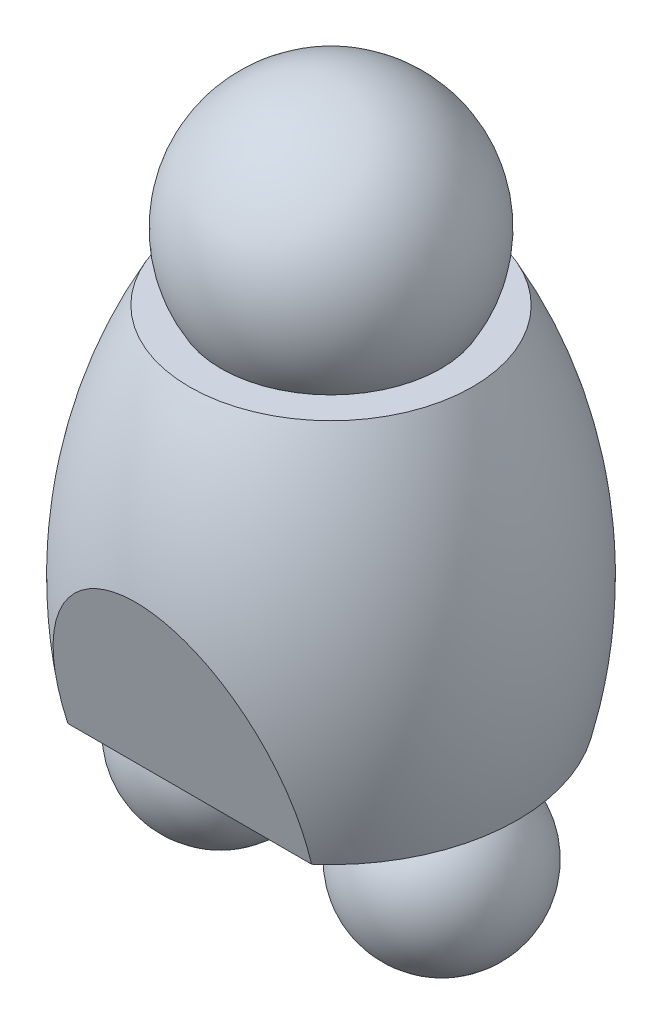
SolidWorks part; units mm, degrees
ref_plane "Front" through (0, 0, 0) normal (0, 0, 1) x (1, 0, 0)
ref_plane "Top" through (0, 0, 0) normal (0, 1, 0) x (1, 0, 0)
ref_plane "Right" through (0, 0, 0) normal (1, 0, 0) x (0, 0, -1)
sketch "Sketch1" plane through (0, 0, 0) normal (0, 0, 1) x (1, 0, 0)
  line L0 (0, 64.0999) -> (0, -73.9034) construction
  line L1 (0, 17.399) -> (0, -17.399)
  line L2 (0, 17.399) -> (13.97, 17.399)
  line L3 (0, -17.399) -> (18.415, -17.399)
  arc A0 (18.415, -17.399) -> (13.97, 17.399) centre (-28.4956, -5.7083) ccw
  point P5 (0, 0)
  dimension "D1" = 34.798
  dimension "D2" = 36.83
  dimension "D3" = 27.94
revolve "Base-Revolve" add sketch "Sketch1" angle 360 about L0
sketch "Sketch2" plane through (0, 0, 0) normal (1, 0, 0) x (0, 0, -1)
  line L2 (-13.944, -17.399) -> (-19.2864, 1.651)
  line L4 (-19.2864, 1.651) -> (-22.8418, 1.651)
  line L5 (-22.8418, 1.651) -> (-22.8418, -17.8942)
  line L7 (19.796, -3.429) -> (22.7378, -3.429)
  line L8 (-22.8418, -17.8942) -> (-13.944, -17.8942)
  line L9 (-13.944, -17.8942) -> (-13.944, -17.399)
  line L10 (22.7378, -3.429) -> (22.7378, -17.8942)
  line L11 (19.796, -3.429) -> (14.0946, -17.399)
  line L12 (22.7378, -17.8942) -> (14.0946, -17.8942)
  line L13 (14.0946, -17.8942) -> (14.0946, -17.399)
extrude "Cut-Extrude1" cut sketch "Sketch2" against normal mid plane 31.9537
sketch "Sketch3" plane through (0, 0, 0) normal (0, 0, 1) x (1, 0, 0)
  line L0 (0, 0) -> (0, 19.8525) construction
  line L1 (0, 64.0999) -> (0, -73.9034) construction
  line L2 (-12.0282, -17.399) -> (12.0282, -17.399) construction
  line L3 (0, 36.703) -> (0, 11.303)
  arc A0 (0, 11.303) -> (0, 36.703) centre (0, 24.003) ccw
  dimension "D1" = 25.4
  dimension "D2" = 41.402
revolve "Boss-Revolve1" add sketch "Sketch3" angle 360 about L0
sketch "Sketch5" plane through (0, 0, 0) normal (0, 0, 1) x (1, 0, 0)
  line L2 (13.97, 17.399) -> (-13.97, 17.399) construction
  line L3 (10.922, -36.2416) -> (10.922, -14.22) construction
  line L6 (10.922, -16.2306) -> (10.922, -32.7914)
  arc A0 (10.922, -32.7914) -> (10.922, -16.2306) centre (10.922, -24.511) ccw
  dimension "D1" = 16.5608
  dimension "D2" = 41.91
  dimension "D3" = 10.922
revolve "Boss-Revolve2" add sketch "Sketch5" angle 360 about L3
mirror "Mirror1" about plane through (0, 0, 0) normal (1, 0, 0) of "Boss-Revolve2"
scale "Scale1" scale about centroid uniform scaling yes scale factor 5.55
